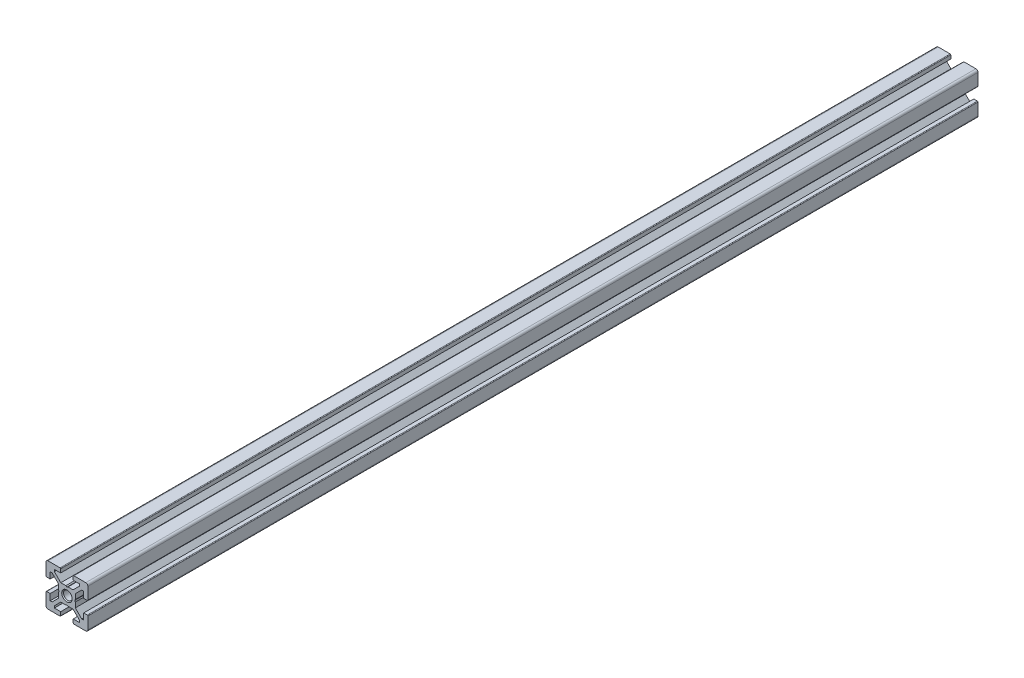
SolidWorks part; units mm, degrees
material "6063-T5"
ref_plane "Front Plane" through (0, 0, 0) normal (0, 0, 1) x (1, 0, 0)
ref_plane "Top Plane" through (0, 0, 0) normal (0, 1, 0) x (1, 0, 0)
ref_plane "Right Plane" through (0, 0, 0) normal (1, 0, 0) x (0, 0, -1)
ref_plane "Plane1" through (0, 0, 0) normal (0, 0, 1) x (1, 0, 0)
sketch "Sketch1" plane through (0, 0, 0) normal (0, 0, 1) x (1, 0, 0)
  line L0 (-10, 9) -> (-10, 3.3)
  line L1 (-9.7, 3) -> (-8, 3)
  line L2 (-8, 3) -> (-8, 6)
  line L3 (-8, 6) -> (-7.0607, 6)
  line L4 (-7.0607, 6) -> (-4, 2.9393)
  line L5 (-4, 2.9393) -> (-4, 0.5196)
  line L6 (-4, 0.5196) -> (-3.7, 0)
  line L7 (-3.7, 0) -> (-4, -0.5196)
  line L8 (-4, -0.5196) -> (-4, -2.9393)
  line L9 (-4, -2.9393) -> (-7.0607, -6)
  line L10 (-7.0607, -6) -> (-8, -6)
  line L11 (-8, -6) -> (-8, -3)
  line L12 (-8, -3) -> (-9.7, -3)
  line L13 (-10, -3.3) -> (-10, -9)
  line L14 (-9, -10) -> (-3.3, -10)
  line L15 (-3, -9.7) -> (-3, -8)
  line L16 (-3, -8) -> (-6, -8)
  line L17 (-6, -8) -> (-6, -7.0607)
  line L18 (-6, -7.0607) -> (-2.9393, -4)
  line L19 (-2.9393, -4) -> (-0.5196, -4)
  line L20 (-0.5196, -4) -> (0, -3.7)
  line L21 (0, -3.7) -> (0.5196, -4)
  line L22 (0.5196, -4) -> (2.9393, -4)
  line L23 (2.9393, -4) -> (6, -7.0607)
  line L24 (6, -7.0607) -> (6, -8)
  line L25 (6, -8) -> (3, -8)
  line L26 (3, -8) -> (3, -9.7)
  line L27 (3.3, -10) -> (9, -10)
  line L28 (10, -9) -> (10, -3.3)
  line L29 (9.7, -3) -> (8, -3)
  line L30 (8, -3) -> (8, -6)
  line L31 (8, -6) -> (7.0606, -6)
  line L32 (7.0606, -6) -> (4, -2.9393)
  line L33 (4, -2.9393) -> (4, -0.5196)
  line L34 (4, -0.5196) -> (3.7, 0)
  line L35 (3.7, 0) -> (4, 0.5196)
  line L36 (4, 0.5196) -> (4, 2.9393)
  line L37 (4, 2.9393) -> (7.0607, 6)
  line L38 (7.0607, 6) -> (8, 6)
  line L39 (8, 6) -> (8, 3)
  line L40 (8, 3) -> (9.7, 3)
  line L41 (10, 3.3) -> (10, 9)
  line L42 (9, 10) -> (3.3, 10)
  line L43 (3, 9.7) -> (3, 8)
  line L44 (3, 8) -> (6, 8)
  line L45 (6, 8) -> (6, 7.0607)
  line L46 (6, 7.0607) -> (2.9393, 4)
  line L47 (2.9393, 4) -> (0.5196, 4)
  line L48 (0.5196, 4) -> (0, 3.7)
  line L49 (0, 3.7) -> (-0.5196, 4)
  line L50 (-0.5196, 4) -> (-2.9394, 4)
  line L51 (-2.9394, 4) -> (-6, 7.0606)
  line L52 (-6, 7.0606) -> (-6, 8)
  line L53 (-6, 8) -> (-3, 8)
  line L54 (-3, 8) -> (-3, 9.7)
  line L55 (-3.3, 10) -> (-9, 10)
  arc A0 (-10, 3.3) -> (-9.7, 3) centre (-9.7, 3.3) ccw
  arc A1 (-9.7, -3) -> (-10, -3.3) centre (-9.7, -3.3) ccw
  arc A2 (-10, -9) -> (-9, -10) centre (-9, -9) ccw
  arc A3 (-3.3, -10) -> (-3, -9.7) centre (-3.3, -9.7) ccw
  arc A4 (3, -9.7) -> (3.3, -10) centre (3.3, -9.7) ccw
  arc A5 (9, -10) -> (10, -9) centre (9, -9) ccw
  arc A6 (10, -3.3) -> (9.7, -3) centre (9.7, -3.3) ccw
  arc A7 (9.7, 3) -> (10, 3.3) centre (9.7, 3.3) ccw
  arc A8 (10, 9) -> (9, 10) centre (9, 9) ccw
  arc A9 (3.3, 10) -> (3, 9.7) centre (3.3, 9.7) ccw
  arc A10 (-3, 9.7) -> (-3.3, 10) centre (-3.3, 9.7) ccw
  arc A11 (-9, 10) -> (-10, 9) centre (-9, 9) ccw
extrude "Boss-Extrude1" add sketch "Sketch1" against normal blind 425
ref_plane "Plane2" through (0, 0, 0) normal (1, 0, 0) x (0, 0, -1)
sketch "Sketch2" plane through (0, 0, 0) normal (1, 0, 0) x (0, 0, -1)
  line L0 (0, 0) -> (0, 2.5)
  line L1 (0, 2.5) -> (0.433, 2.067)
  line L2 (0.433, 2.067) -> (425, 2.067)
  line L3 (425, 2.067) -> (425, 0)
  line L4 (425, 0) -> (0, 0)
  line L5 (425, 0) -> (0, 0) construction
revolve "Cut-Revolve1" cut sketch "Sketch2" angle 360 about L5
cosmetic thread "Cosmetic Thread1" parameters "D1"=15, "D2"=5
cosmetic thread "Cosmetic Thread2" parameters "D1"=15, "D2"=5
ref_plane "Plane3" through (0, 0, 0) normal (1, 0, 0) x (0, 0, -1)
sketch "Sketch3" plane through (0, 0, 0) normal (1, 0, 0) x (0, 0, -1)
  line L0 (0, 0) -> (0, 2.067)
  line L1 (0, 2.067) -> (424.567, 2.067)
  line L2 (424.567, 2.067) -> (425, 2.5)
  line L3 (425, 2.5) -> (425, 0)
  line L4 (425, 0) -> (0, 0)
  line L5 (425, 0) -> (0, 0) construction
revolve "Cut-Revolve2" cut sketch "Sketch3" angle 360 about L5
